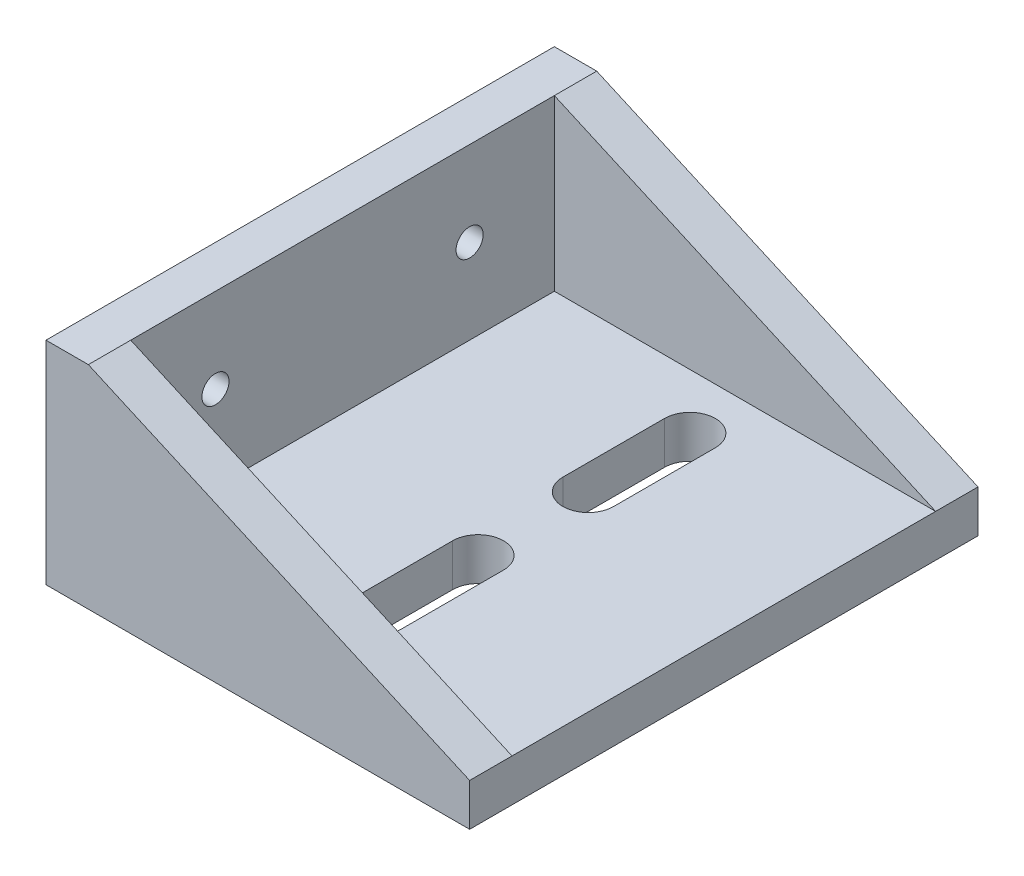
SolidWorks part; units mm, degrees
ref_plane "Ebene vorne" through (0, 0, 0) normal (0, 0, 1) x (1, 0, 0)
ref_plane "Ebene oben" through (0, 0, 0) normal (0, 1, 0) x (1, 0, 0)
ref_plane "Ebene rechts" through (0, 0, 0) normal (1, 0, 0) x (0, 0, -1)
sketch "Sketch1" plane through (0, 0, 0) normal (0, 0, 1) x (1, 0, 0)
  line L0 (0, 0) -> (-50, 0)
  line L1 (-50, 0) -> (-50, 25)
  line L2 (-50, 25) -> (-45, 25)
  line L3 (-45, 25) -> (-45, 5)
  line L4 (-45, 5) -> (0, 5)
  line L5 (0, 5) -> (0, 0)
  dimension "D1" = 5
  dimension "D2" = 5
  dimension "D3" = 50
  dimension "D4" = 25
extrude "Boss-Extrude1" add sketch "Sketch1" along normal blind 60
sketch "Sketch2" plane through (0, 0, 60) normal (0, 0, 1) x (1, 0, 0)
  line L0 (-45, 25) -> (0, 5)
  line L1 (0, 5) -> (-45, 5)
  line L2 (-45, 5) -> (-45, 25)
extrude "Boss-Extrude2" add sketch "Sketch2" against normal blind 5 from offset 0
sketch "Sketch3" plane through (0, 0, 0) normal (0, 0, -1) x (-1, 0, 0)
  line L0 (45, 25) -> (0, 5)
  line L1 (0, 5) -> (45, 5)
  line L2 (45, 5) -> (45, 25)
extrude "Boss-Extrude3" add sketch "Sketch3" against normal blind 5
sketch "Sketch4" plane through (-45, 0, 0) normal (1, 0, 0) x (0, 0, -1)
  line L0 (-30, 25) -> (-30, 5) construction
  line L1 (-55, 25) -> (-5, 25) construction
  line L2 (-55, 5) -> (-5, 5) construction
  circle A0 centre (-45, 15) radius 1.6
  circle A1 centre (-15, 15) radius 1.6
  dimension "D1" = 3.2
  dimension "D2" = 15
  dimension "D3" = 10
extrude "Cut-Extrude1" cut sketch "Sketch4" against normal blind 5
sketch "Sketch5" plane through (0, 5, 0) normal (0, 1, 0) x (1, 0, 0)
  line L0 (-22.5, -23.5) -> (-22.5, -11.5) construction
  line L1 (-25.5, -23.5) -> (-25.5, -11.5)
  line L2 (-19.5, -23.5) -> (-19.5, -11.5)
  line L5 (0, -30) -> (-45, -30) construction
  line L6 (0, -55) -> (0, -5) construction
  line L7 (-45, -55) -> (-45, -5) construction
  line L8 (-22.5, -48.5) -> (-22.5, -36.5) construction
  line L9 (-19.5, -48.5) -> (-19.5, -36.5)
  line L10 (-25.5, -48.5) -> (-25.5, -36.5)
  arc A0 (-25.5, -23.5) -> (-19.5, -23.5) centre (-22.5, -23.5) ccw
  arc A1 (-19.5, -11.5) -> (-25.5, -11.5) centre (-22.5, -11.5) ccw
  arc A2 (-19.5, -48.5) -> (-25.5, -48.5) centre (-22.5, -48.5) cw
  arc A3 (-25.5, -36.5) -> (-19.5, -36.5) centre (-22.5, -36.5) cw
  point P2 (-22.5, -17.5)
  point P11 (0, 0)
  point P12 (0, 0)
  point P20 (-22.5, -42.5)
  point P25 (0, 0)
  point P28 (-22.5, -30)
  dimension "D6" = 6
  dimension "D1" = 12.5
  dimension "D2" = 6
  dimension "D3" = 12.5
  dimension "D4" = 12
  dimension "D5" = 12
extrude "Cut-Extrude2" cut sketch "Sketch5" against normal blind 5
